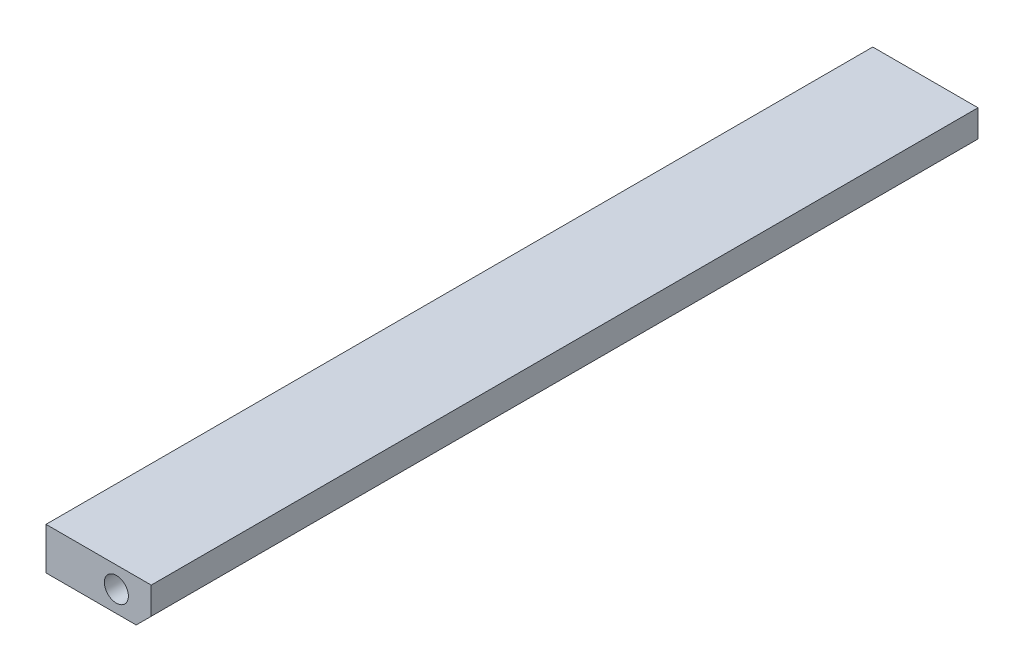
SolidWorks part; units mm, degrees
ref_plane "前视基准面" through (0, 0, 0) normal (0, 0, 1) x (1, 0, 0)
ref_plane "上视基准面" through (0, 0, 0) normal (0, 1, 0) x (1, 0, 0)
ref_plane "右视基准面" through (0, 0, 0) normal (1, 0, 0) x (0, 0, -1)
sketch "草图1" plane through (0, 0, 0) normal (0, 0, 1) x (1, 0, 0)
  line L1 (-17.5, -7) -> (17.5, -7)
  line L2 (-17.5, -7) -> (-17.5, 7)
  line L3 (-17.5, 7) -> (17.5, 7)
  line L4 (17.5, -7) -> (17.5, 7)
  line L5 (-17.5, -7) -> (17.5, 7) construction
  line L6 (-17.5, 7) -> (17.5, -7) construction
  point P0 (0, 0)
  dimension "D1" = 35
  dimension "D2" = 14
extrude "凸台-拉伸1" add sketch "草图1" along normal blind 275
chamfer "倒角1" distance 5 angle 45 1 edges at (17.5, -7, 137.5)
sketch "草图2" plane through (0, 0, 275) normal (0, 0, 1) x (1, 0, 0)
  circle A0 centre (5.9, 0) radius 4
  dimension "D1" = 8
extrude "切除-拉伸1" cut sketch "草图2" against normal blind 10
ref_plane "基准面1" through (0, 0, 137.5) normal (0, 0, -1) x (-1, 0, 0)
mirror "镜向1" about plane through (0, 0, 137.5) normal (0, 0, -1) of "切除-拉伸1"
